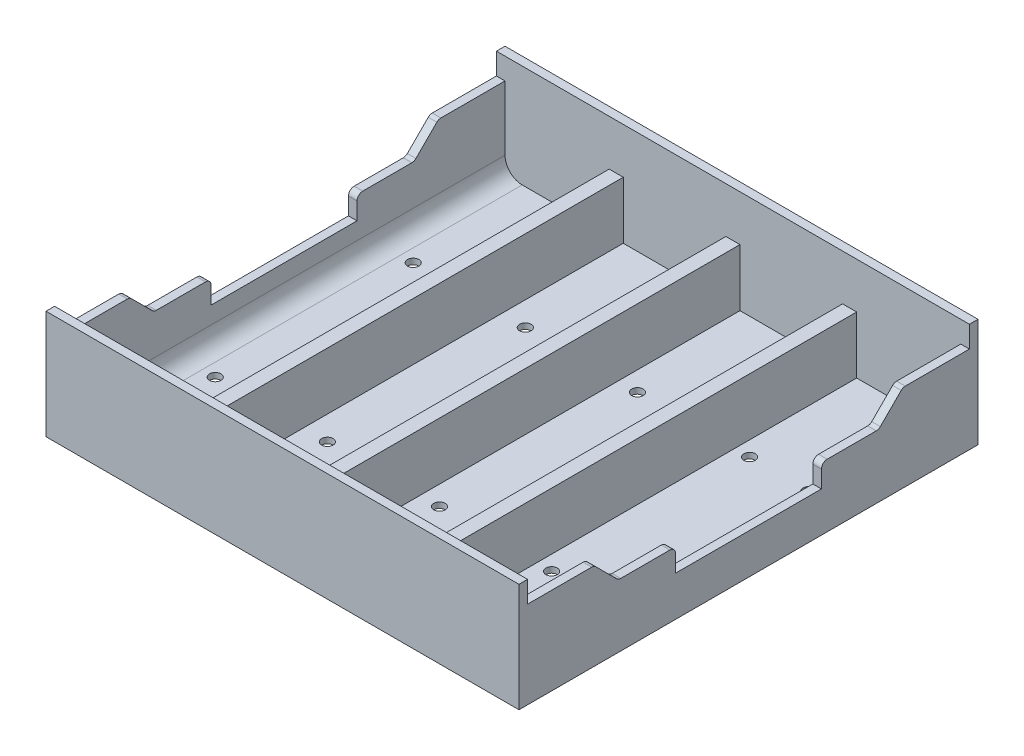
SolidWorks part; units mm, degrees
ref_plane "Front Plane" through (0, 0, 0) normal (0, 0, 1) x (1, 0, 0)
ref_plane "Top Plane" through (0, 0, 0) normal (0, 1, 0) x (1, 0, 0)
ref_plane "Right Plane" through (0, 0, 0) normal (1, 0, 0) x (0, 0, -1)
sketch "Sketch1" plane through (0, 0, 0) normal (0, 1, 0) x (1, 0, 0)
  line L1 (0, 0) -> (82.68, 0)
  line L2 (0, 0) -> (0, 80.24)
  line L3 (0, 80.24) -> (82.68, 80.24)
  line L4 (82.68, 0) -> (82.68, 80.24)
  dimension "D1" = 82.68
  dimension "D2" = 80.24
extrude "Boss-Extrude1" add sketch "Sketch1" along normal blind 19
sketch "Sketch2" plane through (0, 19, 0) normal (0, 1, 0) x (1, 0, 0)
  line L8 (1.5, 78.74) -> (1.5, 1.5)
  line L9 (1.5, 1.5) -> (81.18, 1.5)
  line L10 (81.18, 1.5) -> (81.18, 78.74)
  line L11 (81.18, 78.74) -> (1.5, 78.74)
  line L12 (1.5, 78.74) -> (1.5, 1.5)
  line L13 (1.5, 1.5) -> (81.18, 1.5)
  line L14 (81.18, 1.5) -> (81.18, 78.74)
  line L15 (81.18, 78.74) -> (1.5, 78.74)
  dimension "D1" = 1.5
extrude "Cut-Extrude1" cut sketch "Sketch2" against normal blind 18
sketch "Sketch3" plane through (82.68, 0, 0) normal (1, 0, 0) x (0, 0, -1)
  line L0 (40.12, 19) -> (40.12, 0) construction
  line L1 (0, 19) -> (80.24, 19) construction
  line L2 (0, 0) -> (80.24, 0) construction
  line L3 (27.37, 7) -> (52.87, 7)
  line L4 (27.37, 7) -> (27.37, 10)
  line L5 (26.37, 11) -> (17.7842, 11)
  line L6 (17.0771, 11.2929) -> (13.4203, 14.9497)
  line L7 (12.7131, 15.2426) -> (1.5, 15.2426)
  line L8 (0, 19) -> (0, 0) construction
  line L9 (1.5, 15.2426) -> (1.5, 19)
  line L10 (78.74, 15.2426) -> (78.74, 19)
  line L11 (67.5269, 15.2426) -> (78.74, 15.2426)
  line L12 (63.1629, 11.2929) -> (66.8197, 14.9497)
  line L13 (53.87, 11) -> (62.4558, 11)
  line L14 (52.87, 7) -> (52.87, 10)
  line L15 (1.5, 19) -> (78.74, 19)
  arc A0 (17.7842, 11) -> (17.0771, 11.2929) centre (17.7842, 12) cw
  arc A1 (13.4203, 14.9497) -> (12.7131, 15.2426) centre (12.7131, 14.2426) ccw
  arc A2 (27.37, 10) -> (26.37, 11) centre (26.37, 10) ccw
  arc A3 (66.8197, 14.9497) -> (67.5269, 15.2426) centre (67.5269, 14.2426) cw
  arc A4 (62.4558, 11) -> (63.1629, 11.2929) centre (62.4558, 12) ccw
  arc A5 (52.87, 10) -> (53.87, 11) centre (53.87, 10) cw
  point P17 (17.37, 11)
  point P20 (13.1274, 15.2426)
  point P23 (27.37, 11)
  point P36 (40.12, 7)
  dimension "D9" = 1
  dimension "D1" = 12.75
  dimension "D3" = 7
  dimension "D4" = 4
  dimension "D5" = 10
  dimension "D6" = 45
  dimension "D7" = 6
  dimension "D8" = 1.5
extrude "Cut-Extrude2" cut sketch "Sketch3" against normal through all
ref_plane "Plane1" through (0, 11, 0) normal (0, 1, 0) x (1, 0, 0)
sketch "Sketch5" plane through (0, 11, 0) normal (0, 1, 0) x (1, 0, 0)
  line L0 (20.94, 1.5) -> (20.94, 78.74)
  line L1 (0, 1.5) -> (82.68, 1.5) construction
  line L2 (81.18, 78.74) -> (1.5, 78.74) construction
  line L3 (41.34, 1.5) -> (41.34, 78.74)
  line L4 (1.5, 1.5) -> (81.18, 1.5) construction
  line L5 (82.68, 78.74) -> (0, 78.74) construction
  line L6 (61.74, 1.5) -> (61.74, 78.74)
  line L8 (82.68, 80.24) -> (0, 80.24) construction
  point P16 (41.34, 80.24)
  dimension "D1" = 20.4
  dimension "D2" = 20.4
fillet "Fillet1" radius 3 2 edges at (81.18, 1, -40.12) (1.5, 1, -40.12)
sketch "Sketch6" plane through (0, 0, 0) normal (0, -1, 0) x (-1, 0, 0)
  line L0 (-6.765, 57.42) -> (-75.915, 57.42) construction
  line L7 (-41.34, 80.24) -> (-41.34, 0) construction
  line L8 (-82.68, 80.24) -> (0, 80.24) construction
  line L9 (0, 0) -> (-82.68, 0) construction
  point P12 (-41.34, 40.12)
  point P13 (-6.765, 57.42)
  point P17 (-17.115, 57.42)
  point P20 (-26.365, 57.42)
  point P21 (-36.715, 57.42)
  point P22 (-45.965, 57.42)
  point P26 (-56.315, 57.42)
  point P27 (-65.565, 57.42)
  point P28 (-75.915, 57.42)
  point P32 (-41.34, 57.42)
  dimension "D1" = 17.3
  dimension "D2" = 10.35
  dimension "D4" = 9.25
  dimension "D5" = 10.35
  dimension "D6" = 9.25
  dimension "D7" = 10.35
  dimension "D8" = 9.25
  dimension "D9" = 10.35
hole_wizard "Ø2.0mm Dowel Hole1" positions "Sketch7" profile "Sketch8" hole size "Ø2.0" standard "ANSI Metric" end condition through all
sketch "Sketch7" plane through (0, 0, 0) normal (0, -1, 0) x (-1, 0, 0)
  line L0 (-4.4087, 40.12) -> (-78.2713, 40.12) construction
  line L2 (-41.34, 80.24) -> (-41.34, 0) construction
  point P25 (-6.765, 57.42)
  point P28 (-17.115, 57.42)
  point P31 (-26.365, 57.42)
  point P34 (-36.715, 57.42)
  point P37 (-45.965, 57.42)
  point P40 (-56.315, 57.42)
  point P43 (-65.565, 57.42)
  point P46 (-75.915, 57.42)
  point P57 (-41.34, 40.12)
  point P60 (-75.915, 22.82)
  point P61 (-65.565, 22.82)
  point P62 (-56.315, 22.82)
  point P63 (-45.965, 22.82)
  point P64 (-36.715, 22.82)
  point P65 (-26.365, 22.82)
  point P66 (-17.115, 22.82)
  point P67 (-6.765, 22.82)
sketch "Sketch8" plane through (6.765, 0, -57.42) normal (1, 0, 0) x (0, 0, -1)
  line L0 (0, 0) -> (0, 19)
  line L1 (0, 19) -> (1, 19)
  line L2 (1, 19) -> (1, 0)
  line L5 (1, 0) -> (0, 0)
  line L11 (0, -6.35) -> (0, 107.95) construction
  dimension "Thru Hole Dia." = 2
  dimension "Thru Hole Depth" = 19
rib "Rib1" sketch "Sketch5" sketch "Sketch5" thickness 2.46 extrusion direction normal to sketch draft on no parameters "D1"=2.46
